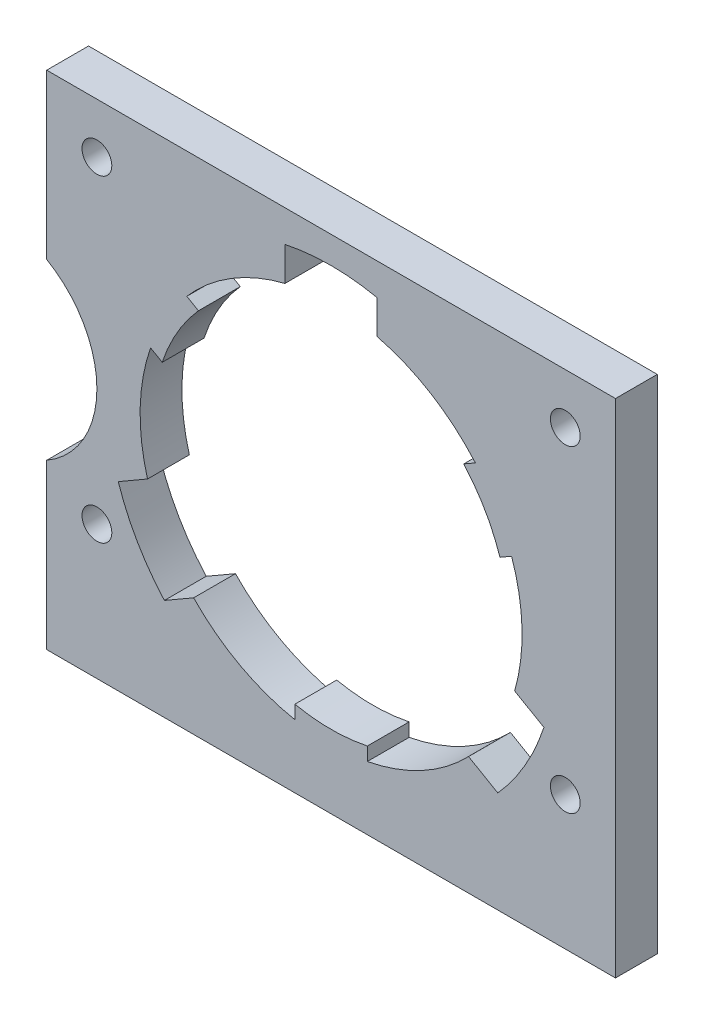
SolidWorks part; units mm, degrees
ref_plane "Front Plane" through (0, 0, 0) normal (0, 0, 1) x (1, 0, 0)
ref_plane "Top Plane" through (0, 0, 0) normal (0, 1, 0) x (1, 0, 0)
ref_plane "Right Plane" through (0, 0, 0) normal (1, 0, 0) x (0, 0, -1)
sketch "Sketch1" plane through (0, 0, 0) normal (0, 0, 1) x (1, 0, 0)
  line L1 (-21.59, 19.05) -> (21.59, 19.05)
  line L2 (-21.59, 19.05) -> (-21.59, -19.05)
  line L3 (-21.59, -19.05) -> (21.59, -19.05)
  line L4 (21.59, 19.05) -> (21.59, -19.05)
  line L5 (-21.59, 19.05) -> (21.59, -19.05) construction
  line L6 (-21.59, -19.05) -> (21.59, 19.05) construction
  point P0 (0, 0)
  dimension "D1" = 43.18
  dimension "D2" = 38.1
extrude "Boss-Extrude1" add sketch "Sketch1" along normal blind 3.175
sketch "Sketch2" plane through (0, 0, 3.175) normal (0, 0, 1) x (1, 0, 0)
  line L0 (-21.59, -19.05) -> (21.59, -19.05) construction
  circle A0 centre (0, 0) radius 14.5
  dimension "D1" = 19.05
  dimension "D2" = 29
extrude "Cut-Extrude1" cut sketch "Sketch2" against normal through all
sketch "Sketch3" plane through (0, 0, 3.175) normal (0, 0, 1) x (1, 0, 0)
  line L0 (-3.5, 16.6358) -> (-3.5, 14.0712)
  line L1 (3.5, 16.6358) -> (3.5, 14.0712)
  arc A0 (3.5, 16.6358) -> (-3.5, 16.6358) centre (0, 0) ccw
  arc A1 (3.5, 14.0712) -> (-3.5, 14.0712) centre (0, 0) ccw
  circle A2 centre (0, 0) radius 14.5 construction
  dimension "D1" = 34
  dimension "D2" = 7
extrude "Cut-Extrude2" cut sketch "Sketch3" against normal through all
pattern_circular "CirPattern1" count 3 over 360 about axis through (0, 0, 0) along (0, 0, 1) of "Cut-Extrude2"
sketch "Sketch4" plane through (0, 0, 3.175) normal (0, 0, 1) x (1, 0, 0)
  line L0 (-2.75, -13.2169) -> (-2.75, -14.2368)
  line L2 (2.75, -13.2169) -> (2.75, -14.2368)
  arc A0 (-2.75, -13.2169) -> (2.75, -13.2169) centre (0, 0) ccw
  arc A1 (-2.75, -14.2368) -> (2.75, -14.2368) centre (0, 0) ccw
  arc A2 (-10.4361, -10.0667) -> (10.4361, -10.0667) centre (0, 0) ccw construction
  dimension "D1" = 27
  dimension "D2" = 5.5
extrude "Boss-Extrude2" add sketch "Sketch4" against normal blind 3.175
pattern_circular "CirPattern2" count 3 over 360 about axis through (0, 0, 0) along (0, 0, 1) of "Boss-Extrude2"
sketch "Sketch5" plane through (0, 0, 3.175) normal (0, 0, 1) x (1, 0, 0)
  line L0 (-21.59, 19.05) -> (-21.59, -19.05) construction
  line L1 (21.59, 19.05) -> (-21.59, 19.05) construction
  line L2 (21.59, -19.05) -> (21.59, 19.05) construction
  line L3 (-21.59, -19.05) -> (21.59, -19.05) construction
  circle A0 centre (-17.78, 15.24) radius 1.1303
  circle A1 centre (17.8363, 15.24) radius 1.1303
  circle A2 centre (17.8363, -8.89) radius 1.1303
  circle A3 centre (-17.78, -8.89) radius 1.1303
  dimension "D1" = 2.2606
  dimension "D2" = 3.81
  dimension "D3" = 3.81
  dimension "D4" = 3.7537
  dimension "D5" = 10.16
extrude "Cut-Extrude3" [suppressed] cut sketch "Sketch5" against normal through all
sketch "Sketch6" plane through (0, 0, 3.175) normal (0, 0, 1) x (1, 0, 0)
  circle A0 centre (-25.4, 0) radius 7.62
  dimension "D1" = 25.4
  dimension "D2" = 15.24
extrude "Cut-Extrude4" cut sketch "Sketch6" against normal through all
hole_wizard "#4-40 Tapped Hole1" positions "Sketch7" profile "Sketch8" tap size "#4-40" standard "ANSI Inch" end condition through all
sketch "Sketch7" plane through (0, 0, 0) normal (0, 0, -1) x (-1, 0, 0)
  line L0 (-21.59, -19.05) -> (-21.59, 19.05) construction
  line L1 (21.59, -19.05) -> (-21.59, -19.05) construction
  line L2 (-21.59, 19.05) -> (21.59, 19.05) construction
  line L3 (21.59, 19.05) -> (21.59, 6.5991) construction
  point P0 (-17.78, 15.24)
  point P2 (-17.78, -8.89)
  point P4 (17.78, -8.89)
  point P6 (17.78, 15.24)
  dimension "D1" = 3.81
  dimension "D2" = 10.16
  dimension "D3" = 3.81
  dimension "D4" = 3.81
sketch "Sketch8" plane through (17.78, 15.24, 0) normal (1, 0, 0) x (0, 1, 0)
  line L0 (0, 0) -> (0, 3.175)
  line L1 (0, 3.175) -> (1.1303, 3.175)
  line L2 (1.1303, 3.175) -> (1.1303, 0)
  line L5 (1.1303, 0) -> (0, 0)
  line L11 (0, -6.35) -> (0, 107.95) construction
  dimension "Thread Major Dia." = 2.2606
  dimension "Thru Tap Drill Depth" = 3.175
